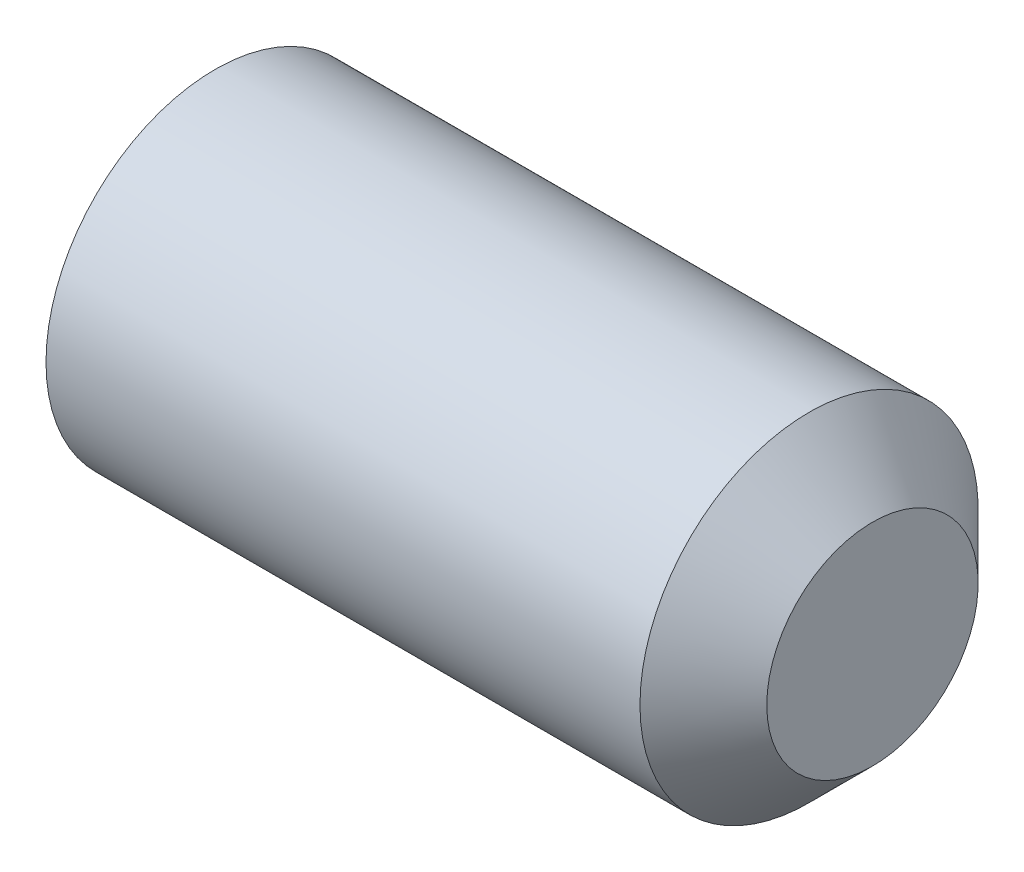
SolidWorks part; units mm, degrees
ref_plane "Plane1" through (0, 0, 0) normal (0, 0, 1) x (1, 0, 0)
ref_plane "Plane2" through (0, 0, 0) normal (0, 1, 0) x (1, 0, 0)
ref_plane "Plane3" through (0, 0, 0) normal (1, 0, 0) x (0, 0, -1)
sketch "BodySke" plane through (0, 0, 0) normal (0, 0, 1) x (1, 0, 0)
  line L0 (0, 0) -> (0, 1.61)
  line L1 (0, 1.61) -> (0.2252, 2)
  line L2 (0.2252, 2) -> (7.25, 2)
  line L3 (7.25, 2) -> (8, 1.25)
  line L4 (8, 0) -> (0, 0)
  line L5 (-12.7, 0) -> (88.9, 0) construction
  line L6 (8, 1.25) -> (8, 0)
  line L7 (8, 1.25) -> (8, 10.775) construction
  line L8 (0, -1.61) -> (0.2252, -2) construction
  line L9 (0.7, 15.875) -> (0.7, -3.175) construction
  line L10 (7.25, -2) -> (8, -1.25) construction
  dimension "Length" = 8
  dimension "Diameter" = 4
  dimension "Drive_ch_ang" = 60
  dimension "Minor_dia" = 3.22
  dimension "Cup_nose_ang" = 45
  dimension "Cup_dia" = 2.5
  dimension "Advance" = 0.7
revolve "BaseBody" add sketch "BodySke" angle 360 about L5
cosmetic thread "ThreadCosmetic" [suppressed] parameters "Thread_minor"=3.22
sketch "Sketch2" plane through (0, 0, 0) normal (-1, 0, 0) x (0, 0, 1)
  line L0 (0.5774, 1) -> (-0.5774, 1)
  line L1 (-0.5774, 1) -> (-1.1547, 0)
  line L2 (0.5774, 1) -> (1.1547, 0)
  line L3 (0.5774, -1) -> (1.1547, 0)
  line L4 (0.5774, -1) -> (-0.5774, -1)
  line L5 (-0.5774, -1) -> (-1.1547, 0)
  dimension "Hex_size" = 2
  dimension "D2" = 1
  dimension "D3" = 1
extrude "Hex" cut sketch "Sketch2" against normal blind 2.5
sketch "ThdSchSke" plane through (0, 0, 0) normal (0, 0, 1) x (1, 0, 0)
  line L0 (0.2252, -1.61) -> (-0.0479, -2)
  line L1 (0.2252, -1.61) -> (0.4982, -2)
  line L2 (0.4982, -2) -> (0.4982, -2.5)
  line L3 (-3.175, 0) -> (5.1513, 0) construction
  line L5 (0.4982, -2.5) -> (-0.0479, -2.5)
  line L6 (-0.0479, -2.5) -> (-0.0479, -2)
  line L8 (0.2252, 2) -> (0.2252, -2) construction
  dimension "Thread_minor" = 3.22
  dimension "Diameter" = 4
  dimension "SideAngle" = 55
  dimension "VeeAngle" = 70
  dimension "Overcut" = 5
revolve "ThreadSchematic" [suppressed] cut sketch "ThdSchSke" angle 360 about L3
pattern_linear "ThdSchPat" [suppressed]
equation "\"D2@Sketch2\" = \"Hex_size@Sketch2\" / 2"
equation "\"D3@Sketch2\" = \"Hex_size@Sketch2\" / 2"
equation "\"Thread_minor@ThreadCosmetic\" = \"Minor_dia@BodySke\""
equation "\"Thread_minor@ThdSchSke\" = \"Thread_minor@ThreadCosmetic\""
equation "\"Diameter@ThdSchSke\" = \"Diameter@BodySke\""
equation "\"Overcut@ThdSchSke\" = \"Diameter@BodySke\" * 1.25"
equation "\"Num_threads@ThdSchPat\" = int( (\"Length@BodySke\" - ( ( ( \"Diameter@BodySke\" - \"Minor_dia@BodySke\" ) * 0.5 ) / tan( \"Drive_ch_ang@BodySke\" * 0.017453292 ) ) - ( ( ( \"Diameter@BodySke\" - \"Cup_dia@BodySke\" ) * 0.5 ) * tan( \"Cup_nose_ang@BodySke\" * 0.017453292 ) ) ) / \"Advance@BodySke\" + 0.999 )  + 1"
equation "\"Advance@ThdSchPat\" = (\"Length@BodySke\" - ( ( ( \"Diameter@BodySke\" - \"Minor_dia@BodySke\" ) * 0.5 ) / tan( \"Drive_ch_ang@BodySke\" * 0.017453292 ) ) - ( ( ( \"Diameter@BodySke\" - \"Cup_dia@BodySke\" ) * 0.5 ) * tan( \"Cup_nose_ang@BodySke\" * 0.017453292 ) ) ) /  (\"Num_threads@ThdSchPat\" - 1) 'relax it"
equation "' \"Num_threads@ThdSchPat\" = \"Num_threads@ThdSchPat\" - sgn( \"Num_threads@ThdSchPat\" - 1) '---chamfered tips only---"
